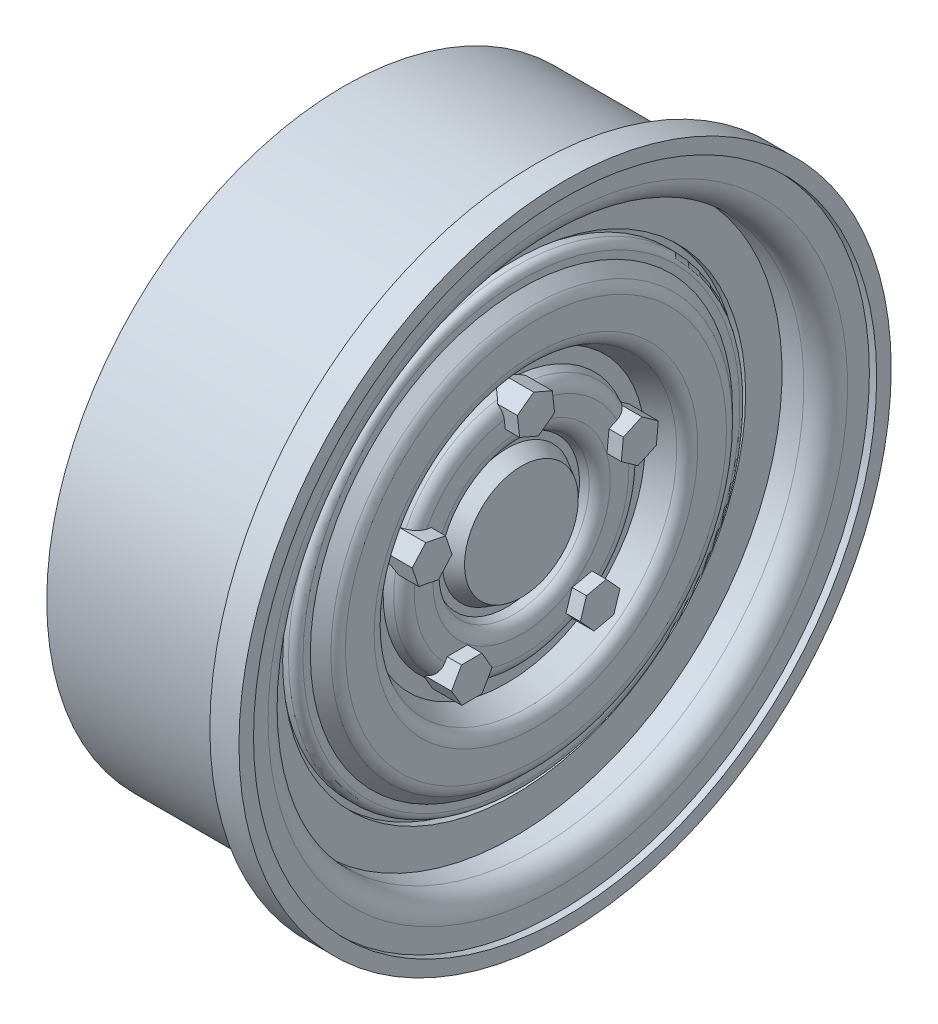
SolidWorks part; units mm, degrees
ref_plane "Front Plane" through (0, 0, 0) normal (0, 0, 1) x (1, 0, 0)
ref_plane "Top Plane" through (0, 0, 0) normal (0, 1, 0) x (1, 0, 0)
ref_plane "Right Plane" through (0, 0, 0) normal (1, 0, 0) x (0, 0, -1)
sketch "Sketch1" plane through (0, 0, 0) normal (0, 0, 1) x (1, 0, 0)
  line L0 (-13.4336, 0) -> (16.2349, 0) construction
  line L1 (5.1385, 22.4) -> (3.1385, 22.4)
  line L2 (3.1385, 22.4) -> (3.1385, 20.4)
  line L3 (3.1385, 20.4) -> (-10.0615, 20.4)
  line L4 (-10.0615, 20.4) -> (-10.0615, 18.4)
  line L5 (-3.5982, 0) -> (1.0403, 0)
  line L7 (5.1385, 22.4) -> (5.1385, 21.4)
  line L8 (5.1385, 21.4) -> (4.6385, 21.4)
  line L9 (4.6385, 21.4) -> (4.6385, 19.9)
  line L10 (3.1385, 18.4) -> (1.6385, 18.4)
  line L11 (1.6385, 18.4) -> (1.6385, 15.9)
  line L12 (1.6385, 15.9) -> (1.1385, 15.9)
  line L13 (1.1385, 15.9) -> (1.1385, 15.5)
  line L26 (1.1385, 15.5) -> (2.1385, 15.5)
  line L27 (2.1385, 15.5) -> (2.1385, 14.5)
  line L30 (3.1385, 10.5) -> (1.1385, 9.5)
  line L35 (1.1385, 9.5) -> (1.1385, 8.5)
  line L36 (1.1385, 8.5) -> (2.1524, 7.9724)
  line L37 (2.1524, 7.9724) -> (2.1524, 5.4724)
  line L38 (2.1524, 5.4724) -> (1.1524, 4.9724)
  line L42 (2.1385, 14.5) -> (3.1385, 13.5)
  line L43 (3.1385, 13.5) -> (3.1385, 10.5)
  line L44 (1.1524, 4.9724) -> (1.1524, 4.4727)
  line L45 (1.1524, 4.4727) -> (2.1385, 3.9079)
  line L46 (2.1385, 3.9079) -> (2.1385, 0)
  line L47 (2.1385, 0) -> (1.0403, 0)
  line L48 (-10.0615, 18.4) -> (-3.5982, 18.4)
  line L53 (-3.5982, 5.6) -> (-3.5982, 0)
  line L54 (-3.5982, 5.6) -> (-10.0615, 5.6)
  line L55 (-10.0615, 5.6) -> (-10.0615, 7.6)
  line L56 (-10.0615, 7.6) -> (-3.5982, 7.6)
  line L57 (-3.5982, 7.6) -> (-3.5982, 18.4)
  arc A0 (4.6385, 19.9) -> (3.1385, 18.4) centre (3.1385, 19.9) cw
  point P29 (4.6385, 18.4)
  dimension "D20" = 1.5
  dimension "D1" = 2
  dimension "D2" = 2
  dimension "D3" = 44.8
  dimension "D4" = 40.8
  dimension "D5" = 13.2
  dimension "D6" = 1
  dimension "D7" = 3
  dimension "D8" = 0.5
  dimension "D9" = 3
  dimension "D10" = 2.5
  dimension "D11" = 0.4
  dimension "D12" = 0.5
  dimension "D13" = 1
  dimension "D14" = 1
  dimension "D15" = 3
  dimension "D16" = 1
  dimension "D17" = 1
  dimension "D18" = 1
  dimension "D19" = 2
  dimension "D21" = 2.5
  dimension "D22" = 2
  dimension "D23" = 11.2
  dimension "D24" = 2
revolve "Revolve1" add sketch "Sketch1" angle 360 about L0
fillet "Fillet1" radius 0.5 1 edges at (2.1385, 0, 15.5)
fillet "Fillet2" radius 1 2 edges at (3.1385, 0, 10.5) (3.1385, 0, 13.5)
fillet "Fillet3" radius 1 2 edges at (2.1524, 0, 5.4724) (2.1524, 0, 7.9724)
sketch "Sketch2" plane through (2.1385, 0, 0) normal (1, 0, 0) x (0, 0, -1)
  line L0 (0, 7.5) -> (0, -7.5) construction
  line L1 (-7.5, 0) -> (7.5, 0) construction
  line L2 (6.9975, 0.9303) -> (8.2666, 1.5067)
  line L8 (1.2775, 6.9425) -> (1.1216, 8.3276)
  line L9 (1.1216, 8.3276) -> (-0.1559, 8.8851)
  line L10 (-0.1559, 8.8851) -> (-1.2775, 8.0575)
  line L11 (-1.2775, 8.0575) -> (-1.1216, 6.6724)
  line L12 (-1.1216, 6.6724) -> (0.1559, 6.1149)
  line L13 (0.1559, 6.1149) -> (1.2775, 6.9425)
  line L14 (8.2666, 1.5067) -> (8.4021, 2.894)
  line L15 (8.4021, 2.894) -> (7.2684, 3.7049)
  line L16 (7.2684, 3.7049) -> (5.9992, 3.1286)
  line L17 (5.9992, 3.1286) -> (5.8638, 1.7413)
  line L18 (5.8638, 1.7413) -> (6.9975, 0.9303)
  line L19 (3.0471, -6.3675) -> (3.9874, -7.3964)
  line L20 (3.9874, -7.3964) -> (5.3487, -7.0966)
  line L21 (5.3487, -7.0966) -> (5.7696, -5.7678)
  line L22 (5.7696, -5.7678) -> (4.8293, -4.7388)
  line L23 (4.8293, -4.7388) -> (3.4681, -5.0387)
  line L24 (3.4681, -5.0387) -> (3.0471, -6.3675)
  line L25 (-5.1142, -4.8657) -> (-5.8022, -6.0779)
  line L26 (-5.8022, -6.0779) -> (-5.0964, -7.2799)
  line L27 (-5.0964, -7.2799) -> (-3.7026, -7.2696)
  line L28 (-3.7026, -7.2696) -> (-3.0145, -6.0573)
  line L29 (-3.0145, -6.0573) -> (-3.7204, -4.8554)
  line L30 (-3.7204, -4.8554) -> (-5.1142, -4.8657)
  line L31 (-6.2079, 3.3603) -> (-7.5734, 3.6401)
  line L32 (-7.5734, 3.6401) -> (-8.4985, 2.5974)
  line L33 (-8.4985, 2.5974) -> (-8.058, 1.2749)
  line L34 (-8.058, 1.2749) -> (-6.6924, 0.9952)
  line L35 (-6.6924, 0.9952) -> (-5.7674, 2.0379)
  line L36 (-5.7674, 2.0379) -> (-6.2079, 3.3603)
  circle A0 centre (0, 0) radius 7.5 construction
  circle A6 centre (0, 7.5) radius 1.2071 construction
  point P19 (0, 0)
  point P42 (0, 0)
  dimension "D1" = 15
  dimension "D2" = 5
extrude "Boss-Extrude1" add sketch "Sketch2" against normal blind 2 and the other way blind 1
